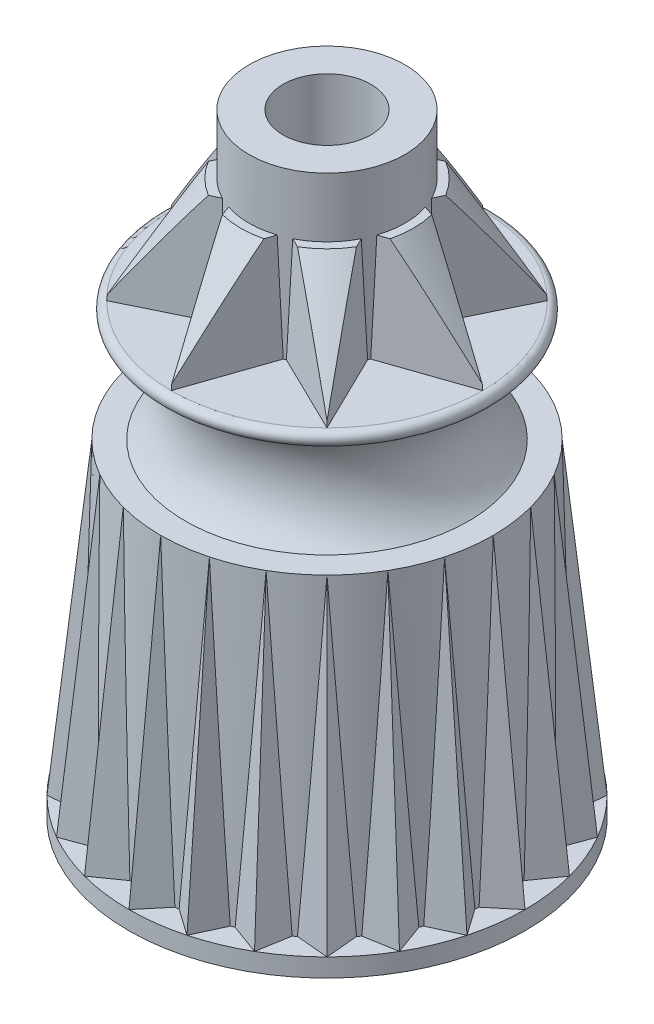
SolidWorks part; units mm, degrees
material "CA"
ref_plane "Front Plane" through (0, 0, 0) normal (0, 0, 1) x (1, 0, 0)
ref_plane "Top Plane" through (0, 0, 0) normal (0, 1, 0) x (1, 0, 0)
ref_plane "Right Plane" through (0, 0, 0) normal (1, 0, 0) x (0, 0, -1)
sketch "Sketch1" plane through (0, 0, 0) normal (0, 1, 0) x (1, 0, 0)
  circle A0 centre (0, 0) radius 8.89
  dimension "D1" = 17.78
extrude "Boss-Extrude1" add sketch "Sketch1" along normal blind 0.8128 draft 1
ref_plane "Plane1" through (0, 14.6304, 0) normal (0, 1, 0) x (1, 0, 0)
sketch "Sketch2" plane through (0, 14.6304, 0) normal (0, 1, 0) x (1, 0, 0)
  circle A0 centre (0, 0) radius 7.4549
  dimension "D1" = 14.9098
sketch "Sketch3" plane through (0, 0.8128, 0) normal (0, 1, 0) x (1, 0, 0)
  circle A0 centre (0, 0) radius 7.8105
  dimension "D1" = 15.621
loft "Loft1" add profiles "Sketch2", "Sketch3"
sketch "Sketch4" plane through (0, 0, 0) normal (1, 0, 0) x (0, 0, -1)
  line L0 (-7.4549, 14.6304) -> (-7.8105, 0.8128) construction
  line L1 (-7.4549, 14.6304) -> (-7.8105, 0.8128) construction
  line L2 (-8.8758, 0.8128) -> (-8.89, 0) construction
  line L3 (-8.8758, 0.8128) -> (-8.89, 0) construction
  line L4 (-8.8758, 0.8128) -> (-7.4549, 14.6304)
ref_plane "Plane2" through (0, 0.8128, 8.8758) normal (0, 0.9948, -0.1023) x (1, 0, 0)
sketch "Sketch5" plane through (0, 0.8128, 8.8758) normal (0, 0.9948, -0.1023) x (1, 0, 0)
  line L0 (0, 0) -> (0, 2.0328) construction
  line L1 (0, 0) -> (0, 1.0597) construction
  line L2 (0, 0) -> (1.2788, 1.524)
  line L3 (0, 0) -> (-1.2788, 1.524)
  line L4 (1.2788, 1.524) -> (-1.2788, 1.524)
  ellipse E0 centre (0, 8.8293) end of major axis (-8.8758, 8.8293) minor radius 8.8293 construction
  dimension "D1" = 80
  dimension "D2" = 1.524
sweep "Sweep1" add profiles "Sketch5" path "Sketch4"
pattern_circular "CirPattern1" count 24 over 360 about axis through (0, 0, 0) along (0, 1, 0) of "Sweep1"
sketch "Sketch7" plane through (0, 0, 0) normal (1, 0, 0) x (0, 0, -1)
  line L0 (0, 0) -> (0, 25.5262) construction
  line L1 (0, 0.8128) -> (0, 14.6304) construction
  line L2 (0, 20.0152) -> (6.985, 20.0152)
  line L3 (6.985, 19.3802) -> (6.35, 19.3802)
  line L4 (1.9295, 14.6304) -> (0, 14.6304) construction
  line L6 (16.7407, 14.6304) -> (0, 14.6304) construction
  line L7 (6.35, 14.6304) -> (0, 14.6304)
  line L8 (0, 14.6304) -> (0, 20.0152)
  arc A0 (6.985, 20.0152) -> (6.985, 19.3802) centre (6.985, 19.6977) cw
  arc A1 (6.35, 19.3802) -> (6.35, 14.6304) centre (8.6591, 17.0053) ccw
  dimension "D4" = 10.6934
  dimension "D1" = 12.7
  dimension "D2" = 0.635
  dimension "D3" = 0.635
  dimension "D5" = 4.7498
revolve "Revolve1" add sketch "Sketch7" angle 360 about L8
sketch "Sketch8" plane through (0, 20.0152, 0) normal (0, 1, 0) x (1, 0, 0)
  circle A0 centre (0, 0) radius 3.4925
  dimension "D1" = 6.985
extrude "Boss-Extrude2" add sketch "Sketch8" along a picked direction on the side of the normal offset from surface (7.4168 mm away) 27.432
sketch "Sketch9" plane through (0, 27.432, 0) normal (0, 1, 0) x (1, 0, 0)
  circle A0 centre (0, 0) radius 1.9685
  dimension "D1" = 3.937
extrude "Cut-Extrude1" cut sketch "Sketch9" against normal through all
sketch "Sketch10" plane through (0, 20.0152, 0) normal (0, 1, 0) x (1, 0, 0)
  line L0 (0, 0) -> (0, -9.673) construction
  line L1 (0, -6.985) -> (-1.5664, -2.436)
  line L2 (0, -6.985) -> (1.5664, -2.436)
  line L3 (-1.5664, -2.436) -> (1.5664, -2.436)
  circle A0 centre (0, 0) radius 6.985 construction
  dimension "D1" = 4.549
  dimension "D2" = 38
extrude "Boss-Extrude3" add sketch "Sketch10" along normal offset from surface 2.667 draft 2
pattern_circular "CirPattern2" count 8 over 360 about axis through (0, 0, 0) along (0, 1, 0) of "Boss-Extrude3"
sketch "Sketch11" plane through (0, 0, 0) normal (1, 0, 0) x (0, 0, -1)
  line L0 (3.4925, 24.765) -> (3.4925, 27.432) construction
  line L1 (3.4925, 24.765) -> (3.4925, 27.432)
  line L2 (6.4755, 24.765) -> (6.985, 20.0152) construction
  line L3 (6.4755, 24.765) -> (6.985, 20.0152) construction
  line L4 (3.4925, 24.765) -> (6.9579, 20.2678) construction
  line L5 (6.9579, 20.2678) -> (7.4659, 20.2678)
  line L6 (7.4659, 20.2678) -> (7.4659, 27.432)
  line L7 (7.4659, 27.432) -> (3.4925, 27.432)
  line L8 (3.4925, 24.765) -> (3.8735, 24.765)
  line L9 (1.5784, 24.765) -> (4.5789, 24.765) construction
  line L10 (3.8735, 24.765) -> (6.9579, 20.2678)
  dimension "D1" = 0.254
  dimension "D2" = 0.508
  dimension "D3" = 0.381
revolve "Cut-Revolve1" cut sketch "Sketch11" angle 360 about axis through (0, 64.7423, 0) along (0, -1, 0)
sketch "Sketch12" plane through (0, 0, 0) normal (1, 0, 0) x (0, 0, -1)
  line L0 (0, 0) -> (0, 28.1928) construction
  line L1 (2.921, 0) -> (3.1941, 15.6464)
  line L2 (3.1941, 15.6464) -> (4.5495, 15.6464)
  line L4 (-8.89, 0) -> (8.89, 0) construction
  line L5 (6.2319, 14.2909) -> (6.6263, 2.9972) construction
  line L6 (2.921, 0) -> (2.921, -2.54)
  line L7 (2.921, -2.54) -> (6.731, -2.54)
  line L8 (6.731, 0) -> (6.731, -2.54)
  line L9 (6.4484, 2.9972) -> (6.491, 1.778)
  line L10 (5.8897, 13.902) -> (6.2705, 2.9972)
  line L11 (6.491, 1.778) -> (6.6689, 1.778)
  line L12 (6.2705, 2.9972) -> (6.4484, 2.9972)
  line L13 (6.6689, 1.778) -> (6.731, 0)
  line L14 (6.0543, 14.2847) -> (6.5533, -0.0062) construction
  line L15 (5.8766, 14.2785) -> (6.3756, -0.0124) construction
  line L16 (5.6417, 13.902) -> (5.8897, 13.902)
  line L17 (6.2319, 14.2909) -> (6.731, 0) construction
  circle A0 centre (0, 0) radius 2.921 construction
  arc A1 (6.35, 19.3802) -> (6.35, 14.6304) centre (8.6591, 17.0053) ccw construction
  arc A2 (6.35, 19.3802) -> (6.35, 14.6304) centre (8.6591, 17.0053) ccw construction
  arc A3 (4.5495, 15.6464) -> (5.6417, 13.902) centre (8.6591, 17.0053) ccw
  circle A4 centre (0, 0) radius 6.731 construction
  arc A5 (5.6417, 20.1086) -> (5.6417, 13.902) centre (8.6591, 17.0053) ccw construction
  dimension "D1" = 5.842
  dimension "D6" = 13.462
  dimension "D3" = 1
  dimension "D4" = 15.6464
  dimension "D5" = 2
  dimension "D7" = 2.54
  dimension "D10" = 1.778
  dimension "D11" = 2.9972
  dimension "D2" = 1.016
  dimension "D8" = 0.1778
  dimension "D9" = 0.1778
revolve "Cut-Revolve2" cut sketch "Sketch12" angle 360 about L0
fillet "Fillet1" radius 0.762 1 edges at (0, 0, -6.731)
sketch "Sketch13" plane through (0, 1.778, 0) normal (0, -1, 0) x (1, 0, 0)
  line L0 (0, -6.491) -> (0, -2.4467)
  line L1 (0, 2.4467) -> (0, 6.491)
  circle A0 centre (0, 0) radius 6.491 construction
  circle A1 centre (0, 0) radius 2.4467 construction
rib "Rib1" sketch "Sketch13" sketch "Sketch13" thickness 1.016 parameters "D1"=1.016, "D3"=1
fillet "Fillet2" radius 0.508 8 edges at (0.508, 1.778, 4.6895) (-0.6093, 7.5791, 2.9919) (-0.508, 1.778, 4.6895) (0.6093, 7.5791, 2.9919) (-0.508, 1.778, -4.6895) (0.508, 1.778, -4.6895)
